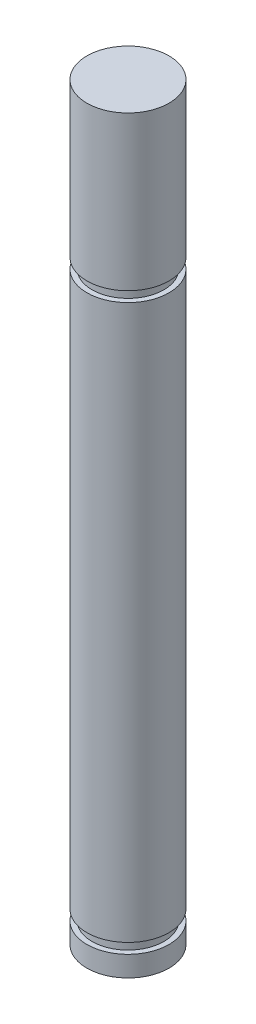
SolidWorks part; units mm, degrees
ref_plane "Front Plane" through (0, 0, 0) normal (0, 0, 1) x (1, 0, 0)
ref_plane "Top Plane" through (0, 0, 0) normal (0, 1, 0) x (1, 0, 0)
ref_plane "Right Plane" through (0, 0, 0) normal (1, 0, 0) x (0, 0, -1)
sketch "Sketch1" plane through (0, 0, 0) normal (0, 1, 0) x (1, 0, 0)
  circle A0 centre (0, 0) radius 4
  dimension "D1" = 8
extrude "Boss-Extrude1" add sketch "Sketch1" along normal blind 73
ref_axis "Axis1" through (0, 73, 0) along (0, -1, 0)
sketch "Sketch2" plane through (0, 0, 0) normal (0, 0, 1) x (1, 0, 0)
  line L0 (4, 73) -> (-4, 73) construction
  line L2 (-4, 73) -> (-4, 0) construction
  line L3 (-4, 58) -> (-4, 57)
  line L4 (-4, 57) -> (-3.5, 57)
  line L5 (-3.5, 57) -> (-3.5, 58)
  line L6 (-3.5, 58) -> (-4, 58)
  line L7 (-4, 0) -> (4, 0) construction
  line L8 (-4, 2) -> (-4, 3)
  line L9 (-4, 3) -> (-3.5, 3)
  line L10 (-3.5, 3) -> (-3.5, 2)
  line L11 (-3.5, 2) -> (-4, 2)
  dimension "D1" = 15
  dimension "D2" = 1
  dimension "D3" = 0.5
  dimension "D4" = 2
  dimension "D5" = 0.5
  dimension "D6" = 1
revolve "Cut-Revolve1" cut sketch "Sketch2" angle 360 about axis through (0, 73, 0) along (0, -1, 0)
